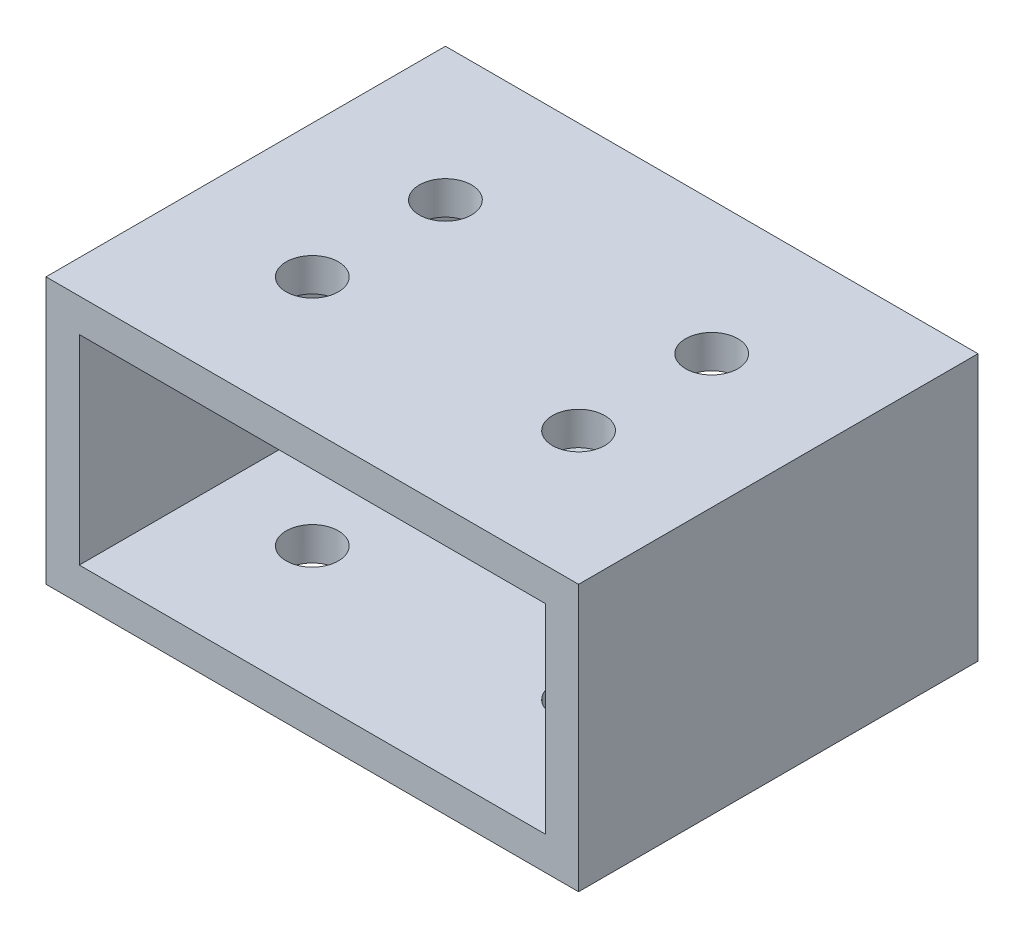
SolidWorks part; units mm, degrees
ref_plane "Front Plane" through (0, 0, 0) normal (0, 0, 1) x (1, 0, 0)
ref_plane "Top Plane" through (0, 0, 0) normal (0, 1, 0) x (1, 0, 0)
ref_plane "Right Plane" through (0, 0, 0) normal (1, 0, 0) x (0, 0, -1)
sketch "Sketch1" plane through (0, 0, 0) normal (0, 0, 1) x (1, 0, 0)
  line L1 (0, 0) -> (50.8, 0)
  line L2 (0, 0) -> (0, 25.4)
  line L3 (0, 25.4) -> (50.8, 25.4)
  line L4 (50.8, 0) -> (50.8, 25.4)
  dimension "D1" = 50.8
  dimension "D2" = 25.4
extrude "Extrude-Thin1" add sketch "Sketch1" along normal mid plane 38.1 thin thin type one direction reverse wall 3.175
sketch "Sketch2" plane through (0, 25.4, 0) normal (0, 1, 0) x (1, 0, 0)
  line L0 (38.1, 19.05) -> (38.1, -19.05) construction
  line L1 (50.8, 19.05) -> (0, 19.05) construction
  line L4 (50.8, -19.05) -> (50.8, 19.05) construction
  line L5 (25.4, 19.05) -> (25.4, -19.05) construction
  line L6 (50.8, -19.05) -> (0, -19.05) construction
  circle A0 centre (38.1, 6.35) radius 2.4892
  circle A1 centre (38.1, -6.35) radius 2.4892
  circle A2 centre (12.7, -6.35) radius 2.4892
  circle A3 centre (12.7, 6.35) radius 2.4892
  dimension "D1" = 4.9784
  dimension "D2" = 12.7
  dimension "D3" = 12.7
  dimension "D4" = 12.7
extrude "Cut-Extrude1" cut sketch "Sketch2" against normal through all
